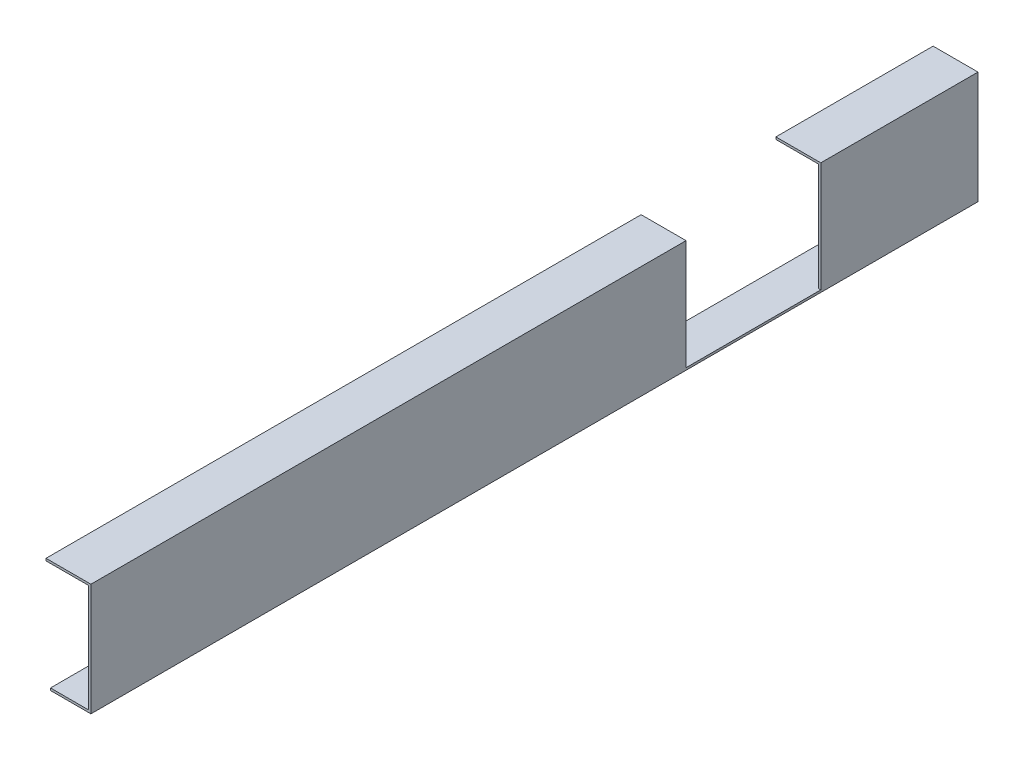
SolidWorks part; units mm, degrees
ref_plane "Front Plane" through (0, 0, 0) normal (0, 0, 1) x (1, 0, 0)
ref_plane "Top Plane" through (0, 0, 0) normal (0, 1, 0) x (1, 0, 0)
ref_plane "Right Plane" through (0, 0, 0) normal (1, 0, 0) x (0, 0, -1)
sketch "Sketch1" plane through (0, 0, 0) normal (0, 0, 1) x (1, 0, 0)
  line L0 (-4, 46.6667) -> (36, 46.6667)
  line L1 (36, 46.6667) -> (36, -53.3333)
  line L2 (36, -53.3333) -> (0, -53.3333)
  line L3 (0, -53.3333) -> (0, -51.3333)
  line L4 (0, -51.3333) -> (34, -51.3333)
  line L5 (34, -51.3333) -> (34, 44.6667)
  line L6 (34, 44.6667) -> (-4, 44.6667)
  line L7 (-4, 44.6667) -> (-4, 46.6667)
  dimension "D1" = 100
  dimension "D2" = 2
  dimension "D3" = 2
  dimension "D4" = 2
extrude "Boss-Extrude1" add sketch "Sketch1" along normal blind 790
sketch "Sketch2" plane through (36, 0, 0) normal (1, 0, 0) x (0, 0, -1)
  line L0 (-790, 46.6667) -> (0, 46.6667) construction
  line L1 (-260, 46.6667) -> (-140, 46.6667)
  line L2 (-260, 46.6667) -> (-260, -51.3333)
  line L3 (-260, -51.3333) -> (-140, -51.3333)
  line L4 (-140, 46.6667) -> (-140, -51.3333)
  line L6 (-790, -53.3333) -> (0, -53.3333) construction
  line L7 (-200, 46.6667) -> (-200, -51.3333) construction
  line L8 (0, -53.3333) -> (0, 46.6667) construction
  dimension "D1" = 200
  dimension "D2" = 120
  dimension "D3" = 2
extrude "Cut-Extrude1" cut sketch "Sketch2" against normal blind 224
